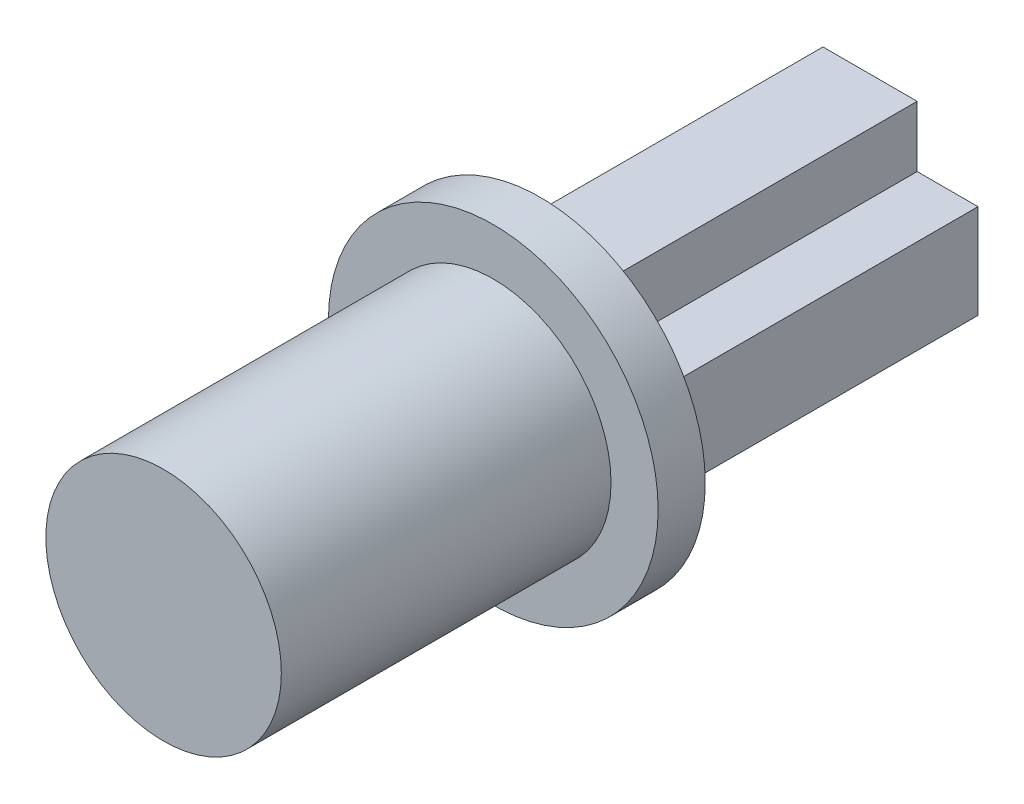
SolidWorks part; units mm, degrees
ref_plane "Front Plane" through (0, 0, 0) normal (0, 0, 1) x (1, 0, 0)
ref_plane "Top Plane" through (0, 0, 0) normal (0, 1, 0) x (1, 0, 0)
ref_plane "Right Plane" through (0, 0, 0) normal (1, 0, 0) x (0, 0, -1)
sketch "Sketch1" plane through (0, 0, 0) normal (0, 0, 1) x (1, 0, 0)
  line L12 (2.2913, -1.0266) -> (1, -1.0266)
  line L13 (2.2913, 0.9734) -> (2.2913, -1.0266)
  line L14 (1, 0.9734) -> (2.2913, 0.9734)
  line L15 (1, 2.2647) -> (1, 0.9734)
  line L16 (-1, 2.2647) -> (1, 2.2647)
  line L17 (-1, 0.9734) -> (-1, 2.2647)
  line L18 (-2.2913, 0.9734) -> (-1, 0.9734)
  line L19 (-2.2913, -1.0266) -> (-2.2913, 0.9734)
  line L20 (-1, -1.0266) -> (-2.2913, -1.0266)
  line L21 (-1, -2.3179) -> (-1, -1.0266)
  line L22 (1, -2.3179) -> (-1, -2.3179)
  line L23 (1, -1.0266) -> (1, -2.3179)
extrude "Boss-Extrude1" add sketch "Sketch1" along normal blind 7
sketch "Sketch2" plane through (0, 0, 7) normal (0, 0, 1) x (1, 0, 0)
  circle A0 centre (0, 0) radius 3.5
  dimension "D1" = 7
extrude "Boss-Extrude2" add sketch "Sketch2" along normal blind 1
sketch "Sketch3" plane through (0, 0, 8) normal (0, 0, 1) x (1, 0, 0)
  circle A0 centre (0, 0) radius 2.5
  dimension "D1" = 5
extrude "Boss-Extrude3" add sketch "Sketch3" along normal blind 7
